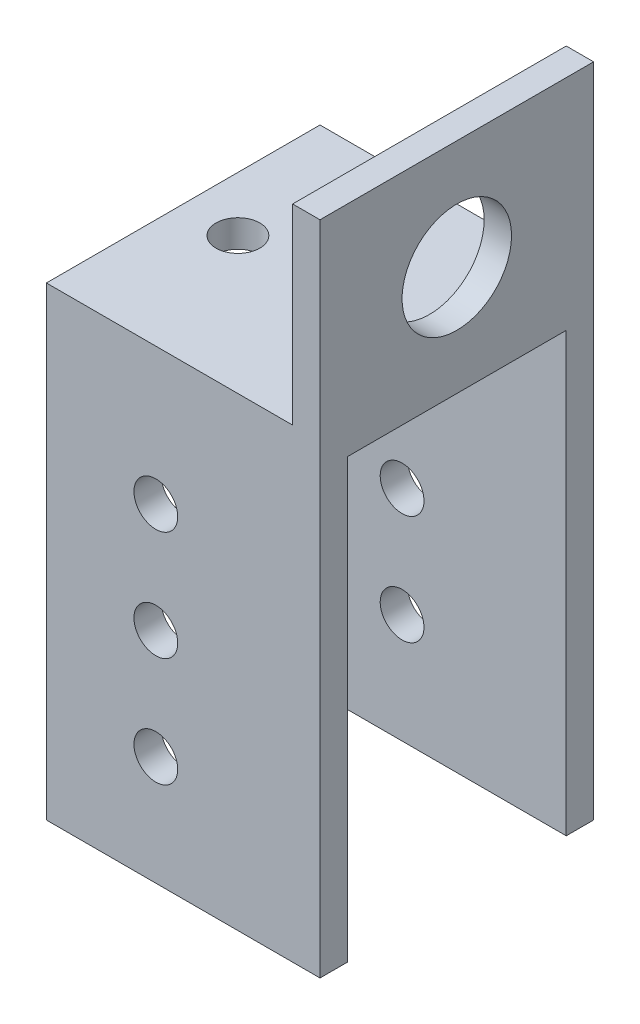
SolidWorks part; units mm, degrees
material "6061-T6 (SS)"
ref_plane "Front Plane" through (0, 0, 0) normal (0, 0, 1) x (1, 0, 0)
ref_plane "Top Plane" through (0, 0, 0) normal (0, 1, 0) x (1, 0, 0)
ref_plane "Right Plane" through (0, 0, 0) normal (1, 0, 0) x (0, 0, -1)
sketch "Sketch8" plane through (0, 0, 0) normal (0, 0, 1) x (1, 0, 0)
  line L1 (-15.875, -38.1) -> (15.875, -38.1)
  line L2 (-15.875, -38.1) -> (-15.875, 38.1)
  line L3 (-15.875, 38.1) -> (15.875, 38.1)
  line L4 (15.875, -38.1) -> (15.875, 38.1)
  line L5 (-15.875, -38.1) -> (15.875, 38.1) construction
  line L6 (-15.875, 38.1) -> (15.875, -38.1) construction
  line L7 (-15.875, 38.1) -> (12.7, 38.1)
  line L8 (-15.875, 38.1) -> (-15.875, 15.875)
  line L9 (-15.875, 15.875) -> (12.7, 15.875)
  line L10 (12.7, 38.1) -> (12.7, 15.875)
  point P0 (0, 0)
  dimension "D1" = 76.2
  dimension "D2" = 31.75
  dimension "D3" = 22.225
  dimension "D4" = 28.575
extrude "Boss-Extrude2" add sketch "Sketch8" along normal blind 31.75 contours L3 L10 L9 L2 L1 L4
sketch "Sketch10" plane through (-15.875, 0, 0) normal (-1, 0, 0) x (0, 0, 1)
  line L0 (31.75, -38.1) -> (31.75, 15.875) construction
  line L1 (3.175, 12.7) -> (28.575, 12.7)
  line L2 (3.175, 12.7) -> (3.175, -38.1)
  line L3 (3.175, -38.1) -> (28.575, -38.1)
  line L4 (28.575, 12.7) -> (28.575, -38.1)
  line L5 (0, -38.1) -> (0, 15.875) construction
  line L6 (31.75, 15.875) -> (0, 15.875) construction
  line L7 (31.75, -38.1) -> (0, -38.1) construction
  dimension "D1" = 3.175
  dimension "D2" = 3.175
  dimension "D3" = 3.175
extrude "Cut-Extrude4" cut sketch "Sketch10" against normal through all
sketch "Sketch11" plane through (0, 15.875, 0) normal (0, 1, 0) x (1, 0, 0)
  line L0 (-15.875, 0) -> (12.7, 0) construction
  line L1 (-15.875, -31.75) -> (-15.875, 0) construction
  circle A0 centre (-9.525, -15.875) radius 2.54
  circle A1 centre (3.175, -15.875) radius 2.54
  point P4 (0, 0)
  point P9 (0, 0)
  dimension "D1" = 5.08
  dimension "D2" = 15.875
  dimension "D3" = 12.7
  dimension "D4" = 6.35
extrude "Cut-Extrude5" cut sketch "Sketch11" against normal up to surface (3.175 mm away) up to face at (0, 12.7, 15.875)
sketch "Sketch12" plane through (0, 0, 31.75) normal (0, 0, 1) x (1, 0, 0)
  line L2 (-15.875, -38.1) -> (-15.875, 15.875) construction
  line L3 (-15.875, -38.1) -> (15.875, -38.1) construction
  circle A0 centre (-3.175, 0) radius 2.54
  circle A1 centre (-3.175, -12.7) radius 2.54
  circle A2 centre (-3.175, -25.4) radius 2.54
  dimension "D1" = 5.08
  dimension "D2" = 12.7
  dimension "D3" = 12.7
  dimension "D4" = 12.7
  dimension "D5" = 12.7
extrude "Cut-Extrude6" cut sketch "Sketch12" against normal up to surface (31.75 mm away) up to face at (4.2333, 5.2917, 0)
sketch "Sketch13" plane through (15.875, 0, 0) normal (1, 0, 0) x (0, 0, -1)
  line L0 (-31.75, 38.1) -> (0, 38.1) construction
  line L1 (-28.575, 12.7) -> (-3.175, 12.7) construction
  circle A0 centre (-15.875, 25.4) radius 6.35
  point P4 (-15.875, 38.1)
  dimension "D1" = 12.7
  dimension "D2" = 12.7
extrude "Cut-Extrude7" cut sketch "Sketch13" against normal up to surface (3.175 mm away) up to face at (12.7, 26.9875, 15.875)
